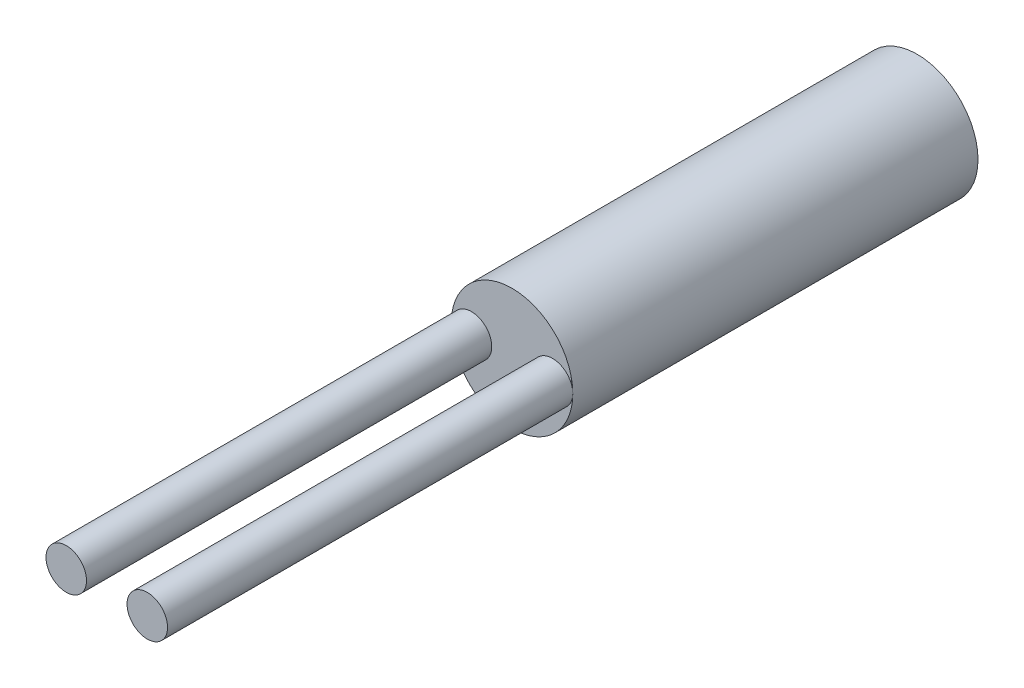
SolidWorks part; units mm, degrees
material "Plain Carbon Steel"
ref_plane "Front Plane" through (0, 0, 0) normal (0, 0, 1) x (1, 0, 0)
ref_plane "Top Plane" through (0, 0, 0) normal (0, 1, 0) x (1, 0, 0)
ref_plane "Right Plane" through (0, 0, 0) normal (1, 0, 0) x (0, 0, -1)
sketch "Sketch1" plane through (0, 0, 0) normal (0, 0, 1) x (1, 0, 0)
  circle A0 centre (0, 0) radius 3
  dimension "D1" = 6
extrude "Boss-Extrude1" add sketch "Sketch1" along normal blind 20
sketch "Sketch2" plane through (0, 0, 20) normal (0, 0, 1) x (1, 0, 0)
  circle A0 centre (-2, 0) radius 1
  circle A1 centre (2, 0) radius 1
  circle A2 centre (0, 0) radius 3 construction
  point P4 (0, 0)
  point P6 (0, 0)
  dimension "D1" = 2
extrude "Boss-Extrude2" add sketch "Sketch2" along normal blind 20
